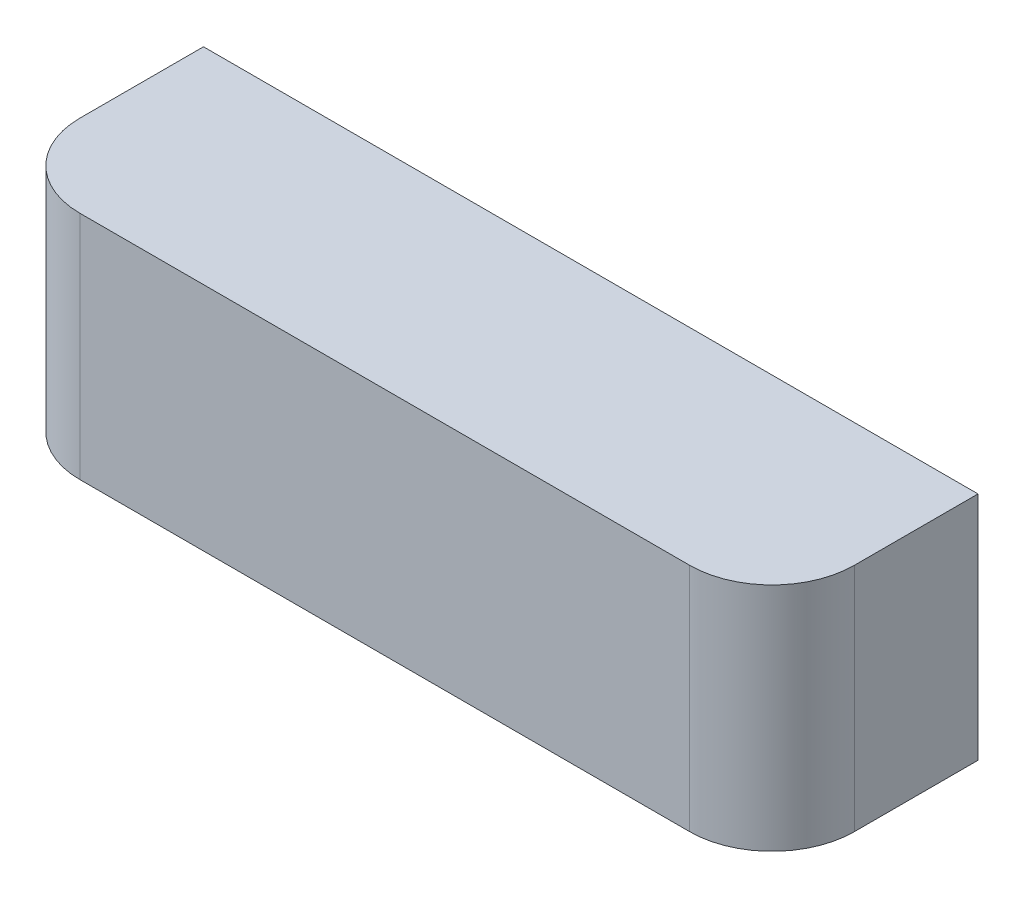
SolidWorks part; units mm, degrees
ref_plane "Front Plane" through (0, 0, 0) normal (0, 0, 1) x (1, 0, 0)
ref_plane "Top Plane" through (0, 0, 0) normal (0, 1, 0) x (1, 0, 0)
ref_plane "Right Plane" through (0, 0, 0) normal (1, 0, 0) x (0, 0, -1)
sketch "Sketch1" plane through (0, 0, 0) normal (0, 0, 1) x (1, 0, 0)
  line L1 (-47, 14) -> (47, 14)
  line L2 (-47, 14) -> (-47, -14)
  line L3 (-47, -14) -> (47, -14)
  line L4 (47, 14) -> (47, -14)
  line L5 (-47, 14) -> (47, -14) construction
  line L6 (-47, -14) -> (47, 14) construction
  point P0 (0, 0)
  dimension "D1" = 94
  dimension "D2" = 28
extrude "Boss-Extrude1" add sketch "Sketch1" along normal blind 25
fillet "Fillet1" radius 10 2 edges at (-47, 0, 25) (47, 0, 25)
sketch "Sketch2" plane through (0, 0, 0) normal (0, 0, -1) x (-1, 0, 0)
  line L0 (47, -14) -> (-47, -14) construction
  line L1 (-20, 1) -> (-7, 1)
  line L2 (-20, 1) -> (-20, -8.5)
  line L3 (-20, -8.5) -> (-7, -8.5)
  line L4 (-7, 1) -> (-7, -8.5)
  line L5 (-20, 1) -> (-7, -8.5) construction
  line L6 (-20, -8.5) -> (-7, 1) construction
  line L7 (-47, -14) -> (-47, 14) construction
  point P0 (-13.5, -3.75)
  point P7 (-20, -3.75)
  dimension "D1" = 5.5
  dimension "D2" = 15
  dimension "D3" = 27
  dimension "D4" = 40
extrude "Boss-Extrude2" add sketch "Sketch2" along normal blind 10
sketch "Sketch3" plane through (0, 0, 0) normal (0, 0, -1) x (-1, 0, 0)
  circle A0 centre (0, 0) radius 17.4019
